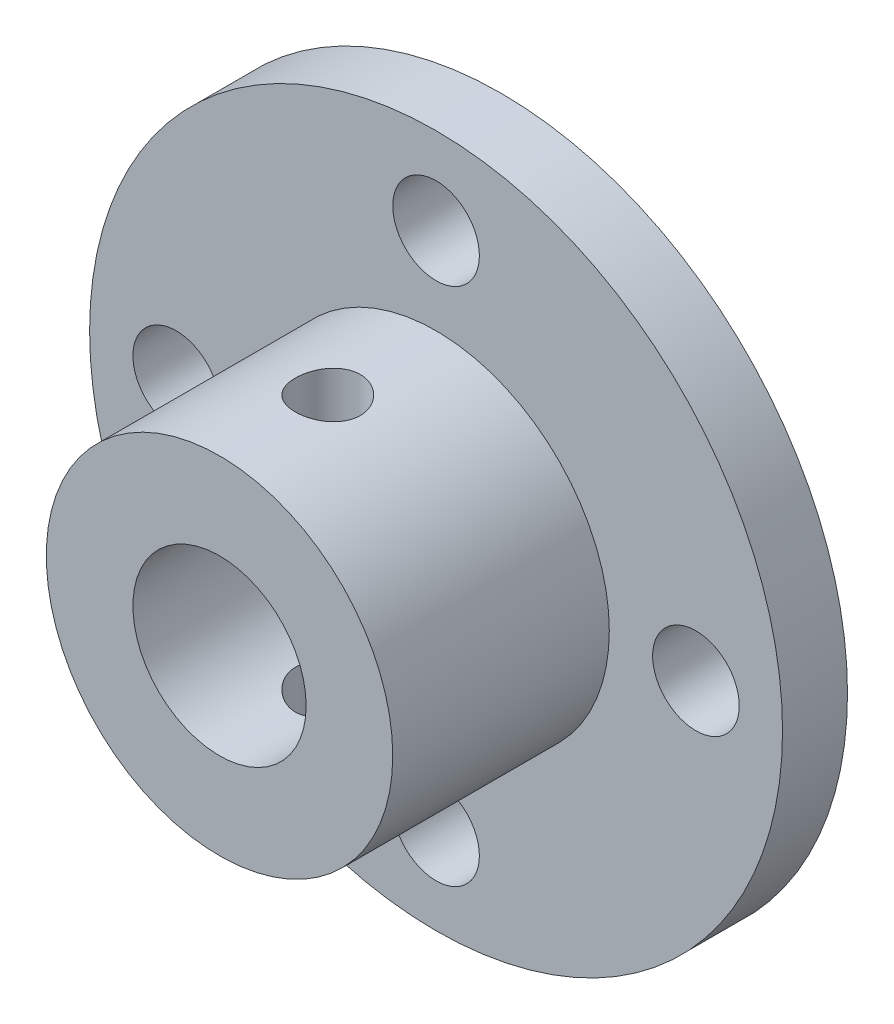
SolidWorks part; units mm, degrees
ref_plane "Piano frontale" through (0, 0, 0) normal (0, 0, 1) x (1, 0, 0)
ref_plane "Piano superiore" through (0, 0, 0) normal (0, 1, 0) x (1, 0, 0)
ref_plane "Piano destro" through (0, 0, 0) normal (1, 0, 0) x (0, 0, -1)
sketch "Schizzo1" plane through (0, 0, 0) normal (0, 0, 1) x (1, 0, 0)
  circle A0 centre (0, 0) radius 16
  dimension "D1" = 32
extrude "Estrusione-Estrusione2" add sketch "Schizzo1" along normal blind 3 contours A0
sketch "Schizzo2" plane through (0, 0, 3) normal (0, 0, 1) x (1, 0, 0)
  circle A0 centre (0, 0) radius 8
  dimension "D1" = 16
extrude "Estrusione-Estrusione3" add sketch "Schizzo2" along normal blind 10
sketch "Schizzo3" plane through (0, 0, 13) normal (0, 0, 1) x (1, 0, 0)
  circle A0 centre (0, 0) radius 4
  circle A1 centre (0, 0) radius 12 construction
  circle A2 centre (12, 0) radius 2
  circle A3 centre (0, 12) radius 2
  circle A4 centre (-12, 0) radius 2
  circle A5 centre (0, -12) radius 2
  dimension "D1" = 8
  dimension "D2" = 24
  dimension "D3" = 4
extrude "Taglio-Estrusione1" cut sketch "Schizzo3" against normal through all both and the other way through all
sketch "Schizzo4" plane through (0, 0, 0) normal (0, 1, 0) x (1, 0, 0)
  line L0 (-8, -13) -> (8, -13) construction
  circle A0 centre (0, -8) radius 1.5
  dimension "D1" = 3
  dimension "D2" = 5
extrude "Taglio-Estrusione2" cut sketch "Schizzo4" against normal through all both and the other way through all
